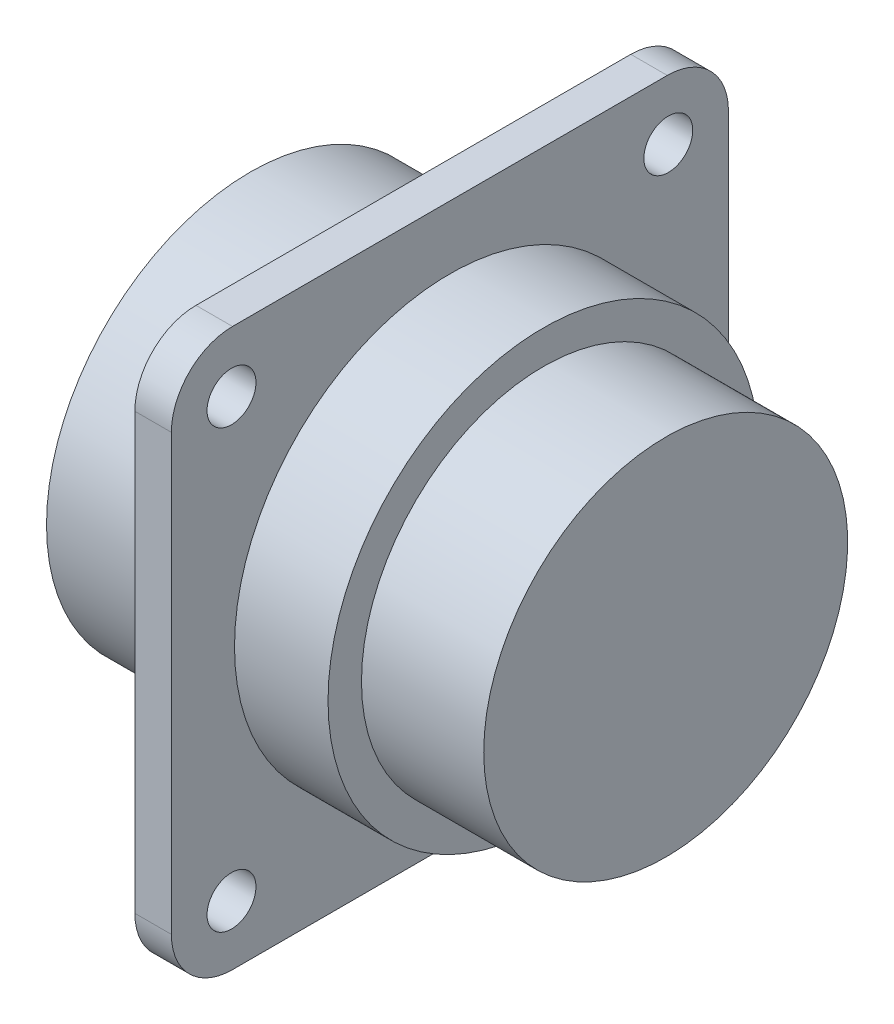
SolidWorks part; units mm, degrees
ref_plane "Front Plane" through (0, 0, 0) normal (0, 0, 1) x (1, 0, 0)
ref_plane "Top Plane" through (0, 0, 0) normal (0, 1, 0) x (1, 0, 0)
ref_plane "Right Plane" through (0, 0, 0) normal (1, 0, 0) x (0, 0, -1)
sketch "Sketch1" plane through (0, 0, 0) normal (0, 0, 1) x (1, 0, 0)
  line L0 (0, 0) -> (62.135, 0) construction
  line L1 (0, 0) -> (0, 13.335)
  line L2 (0, 13.335) -> (10.67, 13.335)
  line L3 (10.67, 13.335) -> (10.67, 30)
  line L4 (10.67, 30) -> (13.06, 30)
  line L5 (13.06, 30) -> (13.06, 14.095)
  line L6 (13.06, 14.095) -> (19.18, 14.095)
  line L7 (19.18, 14.095) -> (19.18, 11.9062)
  line L8 (19.18, 11.9062) -> (27.18, 11.9062)
  line L9 (27.18, 11.9062) -> (27.18, 0)
  line L10 (27.18, 0) -> (0, 0)
  dimension "D1" = 26.67
  dimension "D2" = 28.19
  dimension "D3" = 23.8125
  dimension "D4" = 10.67
  dimension "D5" = 2.39
  dimension "D6" = 60
  dimension "D7" = 27.18
  dimension "D8" = 8
revolve "Revolve1" add sketch "Sketch1" angle 360 about L0
sketch "Sketch2" plane through (10.67, 0, 0) normal (-1, 0, 0) x (0, 0, 1)
  line L0 (-18.225, 18.225) -> (18.225, -18.225) construction
  line L1 (-14.225, 18.225) -> (14.225, 18.225)
  line L2 (-18.225, 14.225) -> (-18.225, -14.225)
  line L3 (-14.225, -18.225) -> (14.225, -18.225)
  line L4 (18.225, 14.225) -> (18.225, -14.225)
  line L5 (-14.29, -14.29) -> (14.29, 14.29) construction
  circle A0 centre (-14.29, 14.29) radius 1.6
  circle A1 centre (14.29, 14.29) radius 1.6
  circle A2 centre (14.29, -14.29) radius 1.6
  circle A3 centre (-14.29, -14.29) radius 1.6
  arc A4 (14.225, 18.225) -> (18.225, 14.225) centre (14.225, 14.225) cw
  arc A5 (14.225, -18.225) -> (18.225, -14.225) centre (14.225, -14.225) ccw
  arc A6 (-18.225, -14.225) -> (-14.225, -18.225) centre (-14.225, -14.225) ccw
  arc A7 (-14.225, 18.225) -> (-18.225, 14.225) centre (-14.225, 14.225) ccw
  dimension "D5" = 3.2
  dimension "D6" = 4
  dimension "D1" = 36.45
  dimension "D2" = 36.45
  dimension "D3" = 28.58
  dimension "D4" = 28.58
extrude "Cut-Extrude1" cut sketch "Sketch2" against normal blind 10 flip side to cut
sketch "Sketch3" plane through (0, 0, 0) normal (-1, 0, 0) x (0, 0, 1)
  circle A0 centre (0, 0) radius 12
  dimension "D1" = 24
extrude "Cut-Extrude2" cut sketch "Sketch3" against normal blind 10
